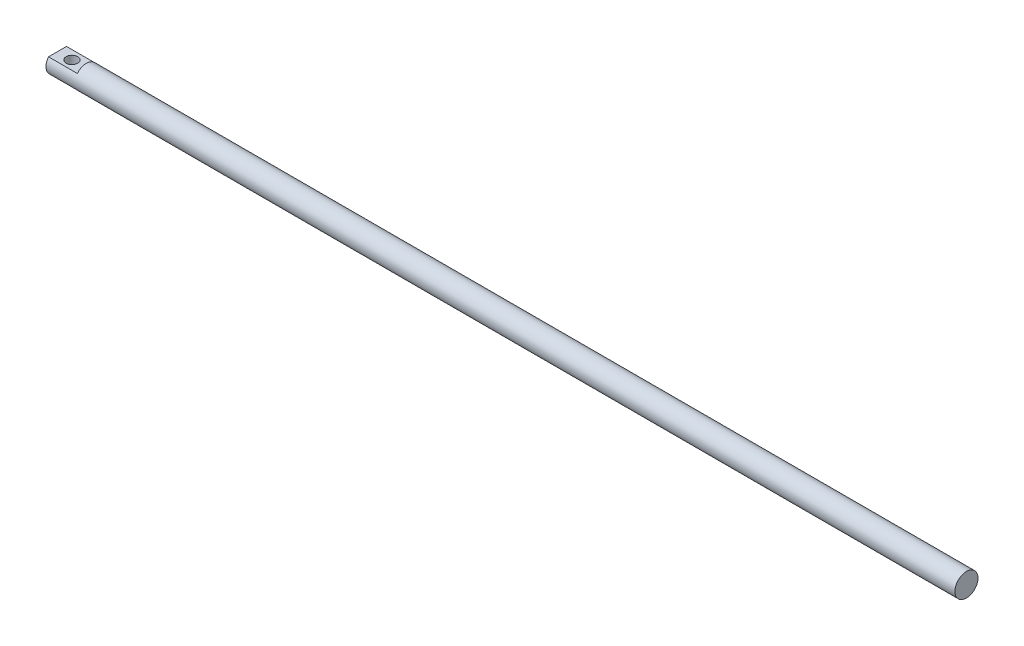
SolidWorks part; units mm, degrees
material "普通碳钢"
ref_plane "前视基准面" through (0, 0, 0) normal (0, 0, 1) x (1, 0, 0)
ref_plane "上视基准面" through (0, 0, 0) normal (0, 1, 0) x (1, 0, 0)
ref_plane "右视基准面" through (0, 0, 0) normal (1, 0, 0) x (0, 0, -1)
sketch "草图1" plane through (0, 0, 0) normal (1, 0, 0) x (0, 0, -1)
  circle A0 centre (0, 0) radius 8
  dimension "D1" = 16
extrude "凸台-拉伸1" add sketch "草图1" along normal blind 630
sketch "草图3" plane through (0, 0, 0) normal (-1, 0, 0) x (0, 0, 1)
  line L5 (-10, -5) -> (10, -5)
  line L6 (-10, -5) -> (-10, 5)
  line L7 (-10, 5) -> (10, 5)
  line L8 (10, -5) -> (10, 5)
  dimension "D1" = 10
  dimension "D2" = 5
  dimension "D3" = 20
  dimension "D4" = 10
extrude "切除-拉伸2" cut sketch "草图3" against normal blind 20 flip side to cut
sketch "草图4" plane through (0, 5, 0) normal (0, 1, 0) x (1, 0, 0)
  line L0 (0, 6.245) -> (0, -6.245) construction
  circle A0 centre (10, 0) radius 4
  dimension "D1" = 8
  dimension "D2" = 10
extrude "切除-拉伸3" cut sketch "草图4" against normal through all
